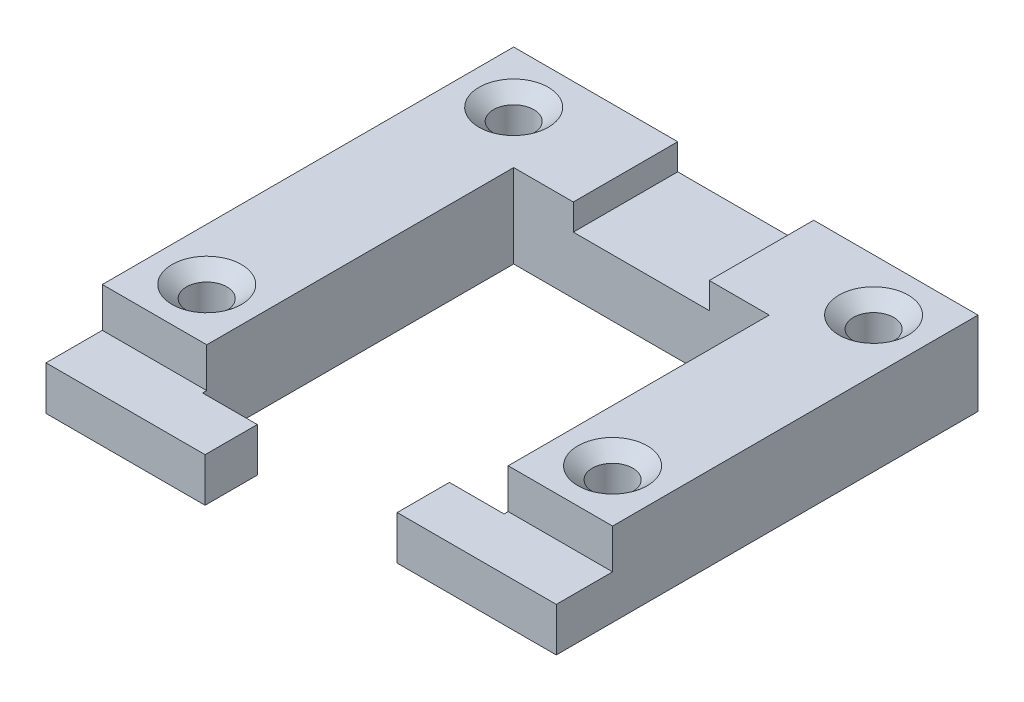
SolidWorks part; units mm, degrees
ref_plane "Front Plane" through (0, 0, 0) normal (0, 0, 1) x (1, 0, 0)
ref_plane "Top Plane" through (0, 0, 0) normal (0, 1, 0) x (1, 0, 0)
ref_plane "Right Plane" through (0, 0, 0) normal (1, 0, 0) x (0, 0, -1)
sketch "Sketch1" plane through (0, 19.05, 0) normal (0, 1, 0) x (1, 0, 0)
  line L0 (15.24, 76.2) -> (15.24, 44.45) construction
  line L1 (-15.24, 38.862) -> (-15.24, 76.2) construction
  line L2 (15.24, 76.2) -> (15.24, 44.45) construction
  line L3 (-15.24, 38.862) -> (-15.24, 76.2) construction
  line L4 (15.54, 76.2) -> (15.54, 44.45)
  line L5 (-15.54, 38.862) -> (-15.54, 76.2)
  line L6 (15.54, 76.2) -> (-15.54, 76.2)
  line L7 (-28.24, 38.862) -> (-28.24, 88.9)
  line L8 (28.24, 88.9) -> (-28.24, 88.9)
  line L9 (28.24, 88.9) -> (28.24, 44.45)
  line L10 (28.24, 44.45) -> (15.54, 44.45)
  line L11 (-15.54, 38.862) -> (-28.24, 38.862)
  dimension "D1" = 0.3
  dimension "D2" = 12.7
extrude "Boss-Extrude1" add sketch "Sketch1" along normal blind 10.16 contours L8 L7 L11 L5 L6 L4 L10 L9
hole_wizard "CSK for #8 Flat Head Machine Screw (100)1" positions "Sketch2" profile "Sketch3" countersink size "#8" standard "ANSI Inch" end condition through all
sketch "Sketch2" plane through (0, 29.21, 0) normal (0, 1, 0) x (1, 0, 0)
  point P0 (-21.89, 82.55)
  point P1 (21.89, 82.55)
  point P2 (-21.89, 45.212)
  point P3 (21.89, 50.8)
sketch "Sketch3" plane through (-21.89, 29.21, -82.55) normal (1, 0, 0) x (0, 0, 1)
  line L0 (0, 0) -> (0, 10.16)
  line L1 (0, 10.16) -> (2.4574, 10.16)
  line L2 (2.4574, 10.16) -> (2.4574, 1.4759)
  line L3 (2.4574, 1.4759) -> (4.2164, 0)
  line L4 (4.2164, 0) -> (0, 0)
  line L5 (-2.4574, 1.4759) -> (-4.2164, 0) construction
  line L6 (0, -6.35) -> (0, 107.95) construction
  dimension "Thru Hole Dia." = 4.9149
  dimension "Thru Hole Depth" = 10.16
  dimension "Near C'Sink Dia." = 8.4328
  dimension "Near C'Sink Angle" = 100
sketch "Sketch5" plane through (0, 0, -88.9) normal (0, 0, -1) x (-1, 0, 0)
  line L0 (-8.255, 35.225) -> (8.285, 35.225) construction
  line L1 (-8.255, 35.225) -> (8.285, 35.225)
  line L2 (-28.24, 29.21) -> (28.24, 29.21) construction
  line L3 (-8.255, 35.225) -> (8.285, 35.225)
  line L4 (-8.255, 35.225) -> (-8.255, 26.035)
  line L5 (-8.255, 26.035) -> (8.285, 26.035)
  line L6 (8.285, 35.225) -> (8.285, 26.035)
  line M7 (28.24, 29.21) -> (-28.24, 29.21)
  dimension "D1" = 3.175
extrude "Cut-Extrude1" cut sketch "Sketch5" against normal through all contours L6 L4 L5 M7
sketch "Sketch6" plane through (0, 19.05, 0) normal (0, -1, 0) x (1, 0, 0)
  line L0 (28.24, -88.9) -> (28.24, -44.45) construction
  line L1 (-28.24, -38.862) -> (-15.54, -38.862)
  line L2 (-28.24, -38.862) -> (-28.24, -38.362)
  line L3 (-28.24, -38.362) -> (-15.54, -38.362)
  line L4 (-15.54, -38.862) -> (-15.54, -38.362)
  line L5 (-28.24, -38.362) -> (-8.89, -38.362)
  line L6 (-28.24, -38.362) -> (-28.24, -32.012)
  line L7 (-28.24, -32.012) -> (-8.89, -32.012)
  line L8 (-8.89, -38.362) -> (-8.89, -32.012)
  line L9 (15.54, -44.45) -> (28.24, -44.45)
  line L10 (15.54, -44.45) -> (15.54, -43.95)
  line L11 (15.54, -43.95) -> (28.24, -43.95)
  line L12 (28.24, -44.45) -> (28.24, -43.95)
  line L13 (28.24, -43.95) -> (8.89, -43.95)
  line L14 (28.24, -43.95) -> (28.24, -37.6)
  line L15 (28.24, -37.6) -> (8.89, -37.6)
  line L16 (8.89, -43.95) -> (8.89, -37.6)
  line L17 (-15.54, -38.862) -> (-15.54, -76.2) construction
  line L18 (-8.89, -76.2) -> (-8.89, -38.862) construction
  line L19 (8.89, -44.45) -> (8.89, -76.2) construction
  line M13 (28.24, -44.45) -> (15.54, -44.45)
  line M17 (-15.54, -38.862) -> (-28.24, -38.862)
  dimension "D1" = 0.5
  dimension "D2" = 6.35
  dimension "D3" = 0.5
  dimension "D4" = 6.35
extrude "Boss-Extrude2" add sketch "Sketch6" against normal blind 5.334 contours L4 L3 L2 M17 | L5 L8 L7 L6 L3 | L12 L11 L10 M13 | L16 L13 L11 L14 L15
